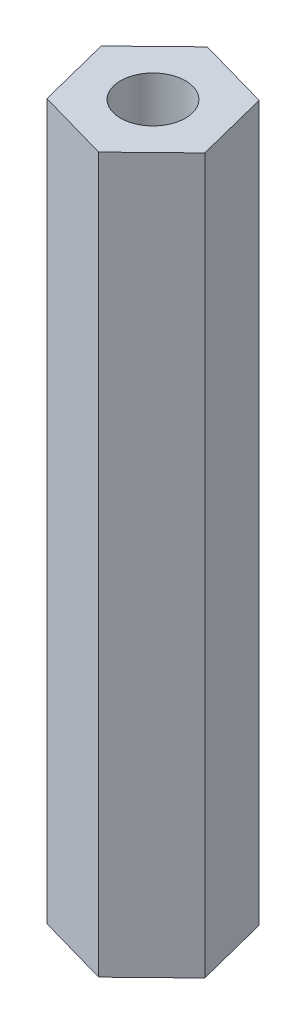
SolidWorks part; units mm, degrees
ref_plane "Front Plane" through (0, 0, 0) normal (0, 0, 1) x (1, 0, 0)
ref_plane "Top Plane" through (0, 0, 0) normal (0, 1, 0) x (1, 0, 0)
ref_plane "Right Plane" through (0, 0, 0) normal (1, 0, 0) x (0, 0, -1)
sketch "Sketch1" plane through (0, 0, 0) normal (0, 1, 0) x (1, 0, 0)
  line L1 (2.6282, 2.5561) -> (-0.8995, 3.5541)
  line L2 (-0.8995, 3.5541) -> (-3.5277, 0.998)
  line L3 (-3.5277, 0.998) -> (-2.6282, -2.5561)
  line L4 (-2.6282, -2.5561) -> (0.8995, -3.5541)
  line L5 (0.8995, -3.5541) -> (3.5277, -0.998)
  line L6 (3.5277, -0.998) -> (2.6282, 2.5561)
  circle A0 centre (0, 0) radius 1.5875
  circle A1 centre (0, 0) radius 3.175 construction
  dimension "D1" = 6.35
  dimension "D2" = 3.175
extrude "Boss-Extrude1" add sketch "Sketch1" along normal blind 34.925
